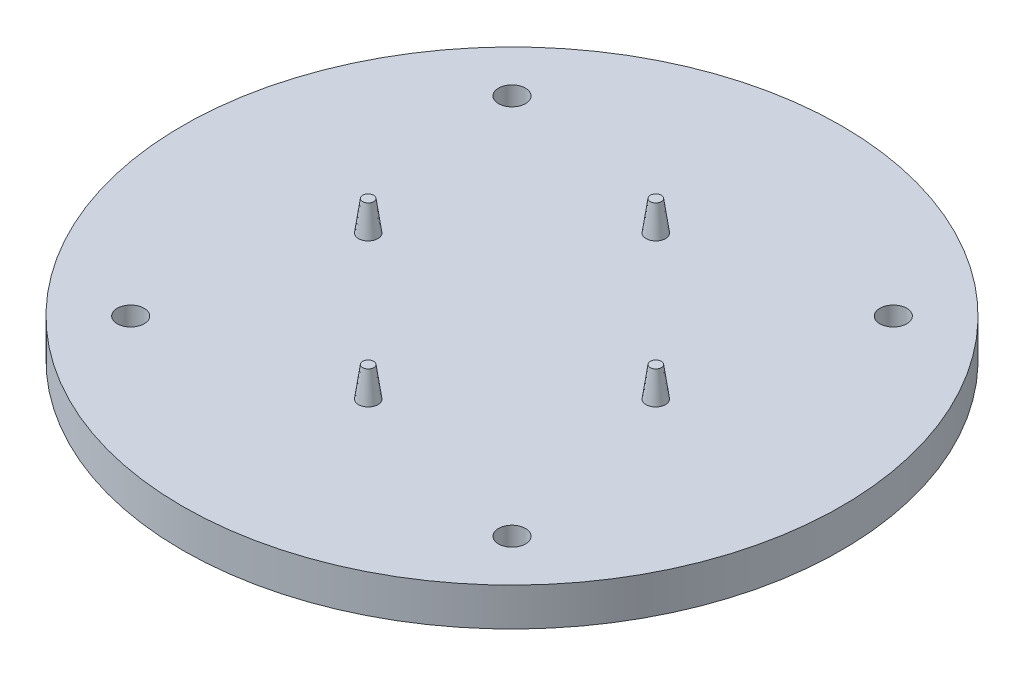
SolidWorks part; units mm, degrees
material "Nylon 101"
ref_plane "Front Plane" through (0, 0, 0) normal (0, 0, 1) x (1, 0, 0)
ref_plane "Top Plane" through (0, 0, 0) normal (0, 1, 0) x (1, 0, 0)
ref_plane "Right Plane" through (0, 0, 0) normal (1, 0, 0) x (0, 0, -1)
sketch "Sketch1" plane through (0, 0, 0) normal (0, 1, 0) x (1, 0, 0)
  circle A0 centre (0, 0) radius 55
  dimension "D1" = 110
extrude "Boss-Extrude1" add sketch "Sketch1" along normal blind 6.35
sketch "Sketch2" plane through (0, 6.35, 0) normal (0, 1, 0) x (1, 0, 0)
  circle A0 centre (0, 0) radius 24 construction
  circle A3 centre (0, -24) radius 1.625
  circle A4 centre (-24, 0) radius 1.625
  circle A5 centre (0, 24) radius 1.625
  circle A6 centre (24, 0) radius 1.625
  point P3 (0, 24)
  point P4 (24, 0)
  point P5 (0, -24)
  point P6 (-24, 0)
  dimension "D1" = 48
  dimension "D2" = 3.25
  dimension "D3" = 4
extrude "Boss-Extrude2" add sketch "Sketch2" along normal blind 5 draft 8
sketch "Sketch3" plane through (0, 6.35, 0) normal (0, 1, 0) x (1, 0, 0)
  line L0 (0, 0) -> (-40.1274, 40.1274) construction
  line L1 (0, 0) -> (-45, 0) construction
  circle A0 centre (0, 0) radius 45
  point P8 (-31.8198, 31.8198)
  point P9 (-31.8198, -31.8198)
  point P10 (31.8198, -31.8198)
  point P11 (31.8198, 31.8198)
  dimension "D1" = 90
  dimension "D2" = 45
  dimension "D3" = 4
hole_wizard "M4 Clearance Hole1" positions "Sketch4" profile "Sketch5" hole size "M4" standard "ANSI Metric" end condition through all
sketch "Sketch4" plane through (0, 6.35, 0) normal (0, 1, 0) x (1, 0, 0)
  point P0 (-31.8198, 31.8198)
  point P3 (31.8198, 31.8198)
  point P6 (31.8198, -31.8198)
  point P9 (-31.8198, -31.8198)
sketch "Sketch5" plane through (-31.8198, 6.35, -31.8198) normal (1, 0, 0) x (0, 0, 1)
  line L0 (0, 0) -> (0, 6.35)
  line L1 (0, 6.35) -> (2.25, 6.35)
  line L2 (2.25, 6.35) -> (2.25, 0)
  line L5 (2.25, 0) -> (0, 0)
  line L11 (0, -6.35) -> (0, 107.95) construction
  dimension "Thru Hole Dia." = 4.5
  dimension "Thru Hole Depth" = 6.35
